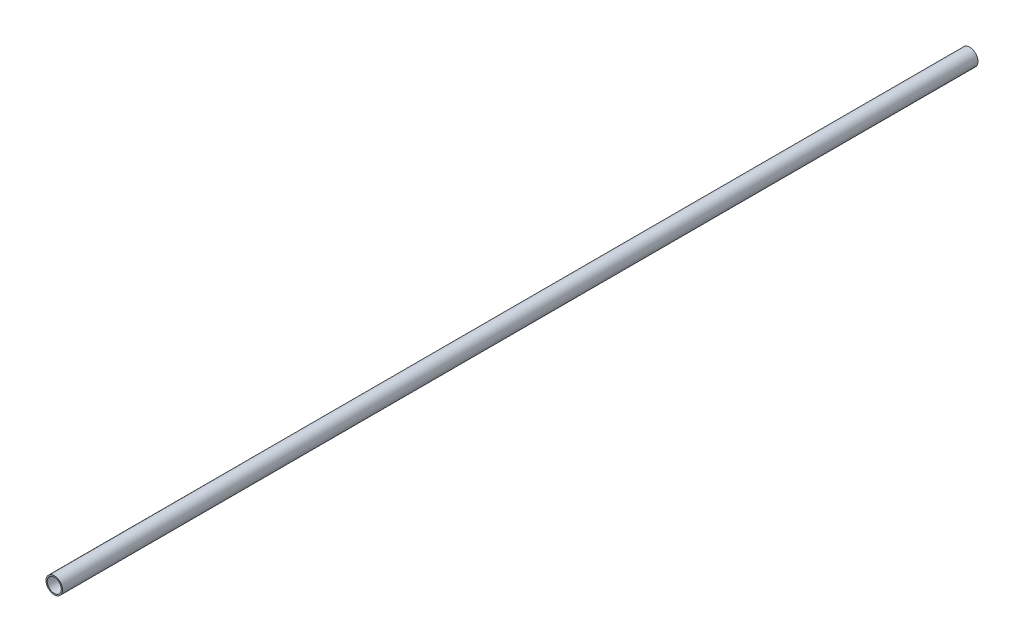
SolidWorks part; units mm, degrees
material "AISI 304"
ref_plane "Front Plane" through (0, 0, 0) normal (0, 0, 1) x (1, 0, 0)
ref_plane "Top Plane" through (0, 0, 0) normal (0, 1, 0) x (1, 0, 0)
ref_plane "Right Plane" through (0, 0, 0) normal (1, 0, 0) x (0, 0, -1)
sketch "Sketch1" plane through (0, 0, 0) normal (0, 0, 1) x (1, 0, 0)
  line L0 (-4.7625, 0) -> (4.7625, 0) construction
  line L1 (0, -4.7625) -> (0, 4.7625) construction
  circle A0 centre (0, 0) radius 4.7625
  circle A1 centre (0, 0) radius 4.0513
  point P4 (0, 0)
  point P9 (0, 0)
  point P10 (-4.0513, 0)
  dimension "ID" = 8.1026
  dimension "OD" = 9.525
  dimension "Wall Thickness" = 0.7112
sketch "Sketch2" plane through (0, 0, 0) normal (1, 0, 0) x (0, 0, -1)
  line L0 (263.525, 4.7625) -> (-263.525, 4.7625) construction
  line L1 (0, 4.7625) -> (0, -4.7625) construction
  point P3 (-254, 4.7625)
  point P4 (0, 4.7625)
  point P5 (254, 4.7625)
  dimension "Length" = 527.05
  dimension "D1" = 9.525
  dimension "D2" = 9.525
sketch "Sketch3" plane through (0, 0, 0) normal (0, 0, 1) x (1, 0, 0)
  line L0 (0, -4.7625) -> (0, 4.7625) construction
  circle A0 centre (0, 0) radius 4.7625
  circle A1 centre (0, 0) radius 4.0513
  circle A2 centre (0, 0) radius 4.0513 construction
extrude "Boss-Extrude1" add sketch "Sketch3" along normal mid plane 527.05
equation "\"D1@Boss-Extrude1\" = \"Length@Sketch2\""
equation "\"D1@Sketch2\"=\"OD@Sketch1\"*1"
equation "\"D2@Sketch2\"=\"D1@Sketch2\""
